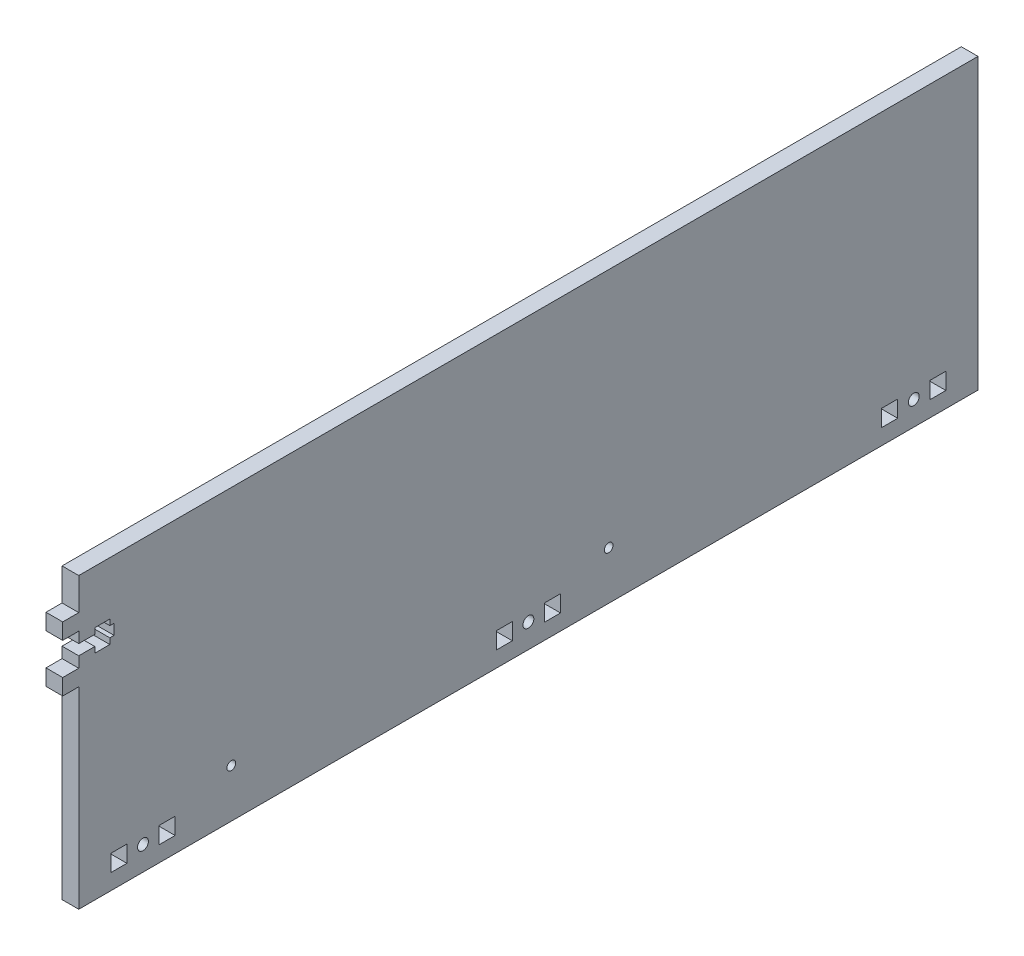
SolidWorks part; units mm, degrees
material "Acrylic (Blue)"
ref_plane "Front Plane" through (0, 0, 0) normal (0, 0, 1) x (1, 0, 0)
ref_plane "Top Plane" through (0, 0, 0) normal (0, 1, 0) x (1, 0, 0)
ref_plane "Right Plane" through (0, 0, 0) normal (1, 0, 0) x (0, 0, -1)
sketch "Sketch1" plane through (0, 0, 0) normal (1, 0, 0) x (0, 0, -1)
  line L0 (-139.7, 12.827) -> (-12.7, 12.827) construction
  line L1 (-177.8, 114.3) -> (177.8, 114.3)
  line L2 (-177.8, 114.3) -> (-177.8, 0)
  line L3 (-177.8, 0) -> (177.8, 0)
  line L4 (177.8, 114.3) -> (177.8, 0)
  line L5 (12.7, 12.827) -> (139.7, 12.827) construction
  line B0 (-146.05, 12.827) -> (-139.7, 12.827)
  line B1 (-139.7, 12.827) -> (-139.7, 6.223)
  line B2 (-139.7, 6.223) -> (-146.05, 6.223)
  line B3 (-146.05, 6.223) -> (-146.05, 12.827)
  line B4 (-165.1, 12.827) -> (-158.75, 12.827)
  line B5 (-158.75, 12.827) -> (-158.75, 6.223)
  line B6 (-158.75, 6.223) -> (-165.1, 6.223)
  line B7 (-165.1, 6.223) -> (-165.1, 12.827)
  circle B8 centre (-152.4, 9.525) radius 2.1526
  line B9 (6.35, 12.827) -> (12.7, 12.827)
  line B10 (12.7, 12.827) -> (12.7, 6.223)
  line B11 (12.7, 6.223) -> (6.35, 6.223)
  line B12 (6.35, 6.223) -> (6.35, 12.827)
  line B13 (-12.7, 12.827) -> (-6.35, 12.827)
  line B14 (-6.35, 12.827) -> (-6.35, 6.223)
  line B15 (-6.35, 6.223) -> (-12.7, 6.223)
  line B16 (-12.7, 6.223) -> (-12.7, 12.827)
  circle B17 centre (0, 9.525) radius 2.1526
  line B18 (158.75, 12.827) -> (165.1, 12.827)
  line B19 (165.1, 12.827) -> (165.1, 6.223)
  line B20 (165.1, 6.223) -> (158.75, 6.223)
  line B21 (158.75, 6.223) -> (158.75, 12.827)
  line B22 (139.7, 12.827) -> (146.05, 12.827)
  line B23 (146.05, 12.827) -> (146.05, 6.223)
  line B24 (146.05, 6.223) -> (139.7, 6.223)
  line B25 (139.7, 6.223) -> (139.7, 12.827)
  circle B26 centre (152.4, 9.525) radius 2.1526
  dimension "D1" = 114.3
  dimension "D2" = 355.6
  dimension "D3" = 12.7
  dimension "D4" = 12.7
  dimension "D5" = 9.525
sketch_block_instance "BOLT_HOLE-1"
sketch_block "BOLT_HOLE" parameters "D1"=4.3053, "D2"=6.35, "D3"=6.35, "D4"=6.604
sketch_block_instance "BOLT_HOLE-2"
sketch_block_instance "BOLT_HOLE-3"
extrude "Boss-Extrude1" add sketch "Sketch1" along normal blind 6.604
sketch "Sketch4" plane through (0, 0, 0) normal (-1, 0, 0) x (0, 0, 1)
  line L0 (177.8, 114.3) -> (177.8, 0) construction
  line L1 (-177.8, 114.3) -> (177.8, 114.3) construction
  line B0 (177.8, 90.9828) -> (171.45, 90.9828)
  line B1 (171.45, 90.9828) -> (171.45, 93.2688)
  line B2 (171.45, 93.2688) -> (165.5064, 93.2688)
  line B3 (165.5064, 93.2688) -> (165.5064, 90.9828)
  line B4 (165.5064, 90.9828) -> (163.83, 90.9828)
  line B5 (163.83, 90.9828) -> (163.83, 86.8172)
  line B6 (163.83, 86.8172) -> (165.5064, 86.8172)
  line B7 (165.5064, 86.8172) -> (165.5064, 84.5312)
  line B8 (165.5064, 84.5312) -> (171.45, 84.5312)
  line B9 (171.45, 84.5312) -> (171.45, 86.8172)
  line B10 (171.45, 86.8172) -> (177.8, 86.8172)
  line B11 (177.8, 86.8172) -> (177.8, 82.55)
  line B12 (177.8, 82.55) -> (184.15, 82.55)
  line B13 (184.15, 82.55) -> (184.15, 76.2)
  line B14 (184.15, 76.2) -> (177.8, 76.2)
  line B15 (177.8, 90.9828) -> (177.8, 95.25)
  line B16 (177.8, 95.25) -> (184.15, 95.25)
  line B17 (184.15, 95.25) -> (184.15, 101.6)
  line B18 (184.15, 101.6) -> (177.8, 101.6)
  line B19 (177.8, 86.8172) -> (177.8, 90.9828) construction
  dimension "D1" = 12.7
sketch_block_instance "NUT_HOLE-1"
sketch_block "NUT_HOLE" parameters "D1"=6.35, "D2"=4.1656, "D3"=25.4, "D4"=6.35, "D5"=8.7376, "D6"=5.9436, "D7"=6.35, "D8"=20.32
sketch "Sketch5" plane through (0, 0, 0) normal (-1, 0, 0) x (0, 0, 1)
  line L0 (177.8, 90.9828) -> (171.45, 90.9828) construction
  line L1 (171.45, 90.9828) -> (171.45, 93.2688) construction
  line L2 (171.45, 93.2688) -> (165.5064, 93.2688) construction
  line L3 (165.5064, 93.2688) -> (165.5064, 90.9828) construction
  line L4 (165.5064, 90.9828) -> (163.83, 90.9828) construction
  line L5 (163.83, 90.9828) -> (163.83, 86.8172) construction
  line L6 (163.83, 86.8172) -> (165.5064, 86.8172) construction
  line L7 (165.5064, 86.8172) -> (165.5064, 84.5312) construction
  line L8 (165.5064, 84.5312) -> (171.45, 84.5312) construction
  line L9 (171.45, 86.8172) -> (177.8, 86.8172) construction
  line L10 (171.45, 84.5312) -> (171.45, 86.8172) construction
  line L11 (177.8, 90.9828) -> (171.45, 90.9828)
  line L12 (171.45, 90.9828) -> (171.45, 93.2688)
  line L13 (171.45, 93.2688) -> (165.5064, 93.2688)
  line L14 (165.5064, 93.2688) -> (165.5064, 90.9828)
  line L15 (165.5064, 90.9828) -> (163.83, 90.9828)
  line L16 (163.83, 90.9828) -> (163.83, 86.8172)
  line L17 (163.83, 86.8172) -> (165.5064, 86.8172)
  line L18 (165.5064, 86.8172) -> (165.5064, 84.5312)
  line L19 (165.5064, 84.5312) -> (171.45, 84.5312)
  line L20 (171.45, 86.8172) -> (177.8, 86.8172)
  line L21 (171.45, 84.5312) -> (171.45, 86.8172)
  line L22 (177.8, 90.9828) -> (177.8, 86.8172)
extrude "Cut-Extrude1" cut sketch "Sketch5" against normal through all
sketch "Sketch6" plane through (0, 0, 0) normal (-1, 0, 0) x (0, 0, 1)
  line L0 (184.15, 101.6) -> (177.8, 101.6) construction
  line L1 (184.15, 95.25) -> (184.15, 101.6) construction
  line L2 (177.8, 95.25) -> (184.15, 95.25) construction
  line L3 (184.15, 76.2) -> (177.8, 76.2) construction
  line L4 (177.8, 82.55) -> (184.15, 82.55) construction
  line L5 (184.15, 82.55) -> (184.15, 76.2) construction
  line L6 (184.15, 101.6) -> (177.8, 101.6)
  line L7 (184.15, 95.25) -> (184.15, 101.6)
  line L8 (177.8, 95.25) -> (184.15, 95.25)
  line L9 (184.15, 76.2) -> (177.8, 76.2)
  line L10 (177.8, 82.55) -> (184.15, 82.55)
  line L11 (184.15, 82.55) -> (184.15, 76.2)
  line L12 (177.8, 101.6) -> (177.8, 95.25)
  line L13 (177.8, 82.55) -> (177.8, 76.2)
extrude "Boss-Extrude2" add sketch "Sketch6" against normal up to surface (6.604 mm away) up to face at (6.604, 80.9625, 126.9428)
hole_wizard "CSK for #8 Flat Head Socket Cap Screw1" positions "Sketch8" profile "Sketch7" countersink size "#8" standard "ANSI Inch" end condition through all
sketch "Sketch8" plane through (0, 0, 0) normal (-1, 0, 0) x (0, 0, 1)
  circle A0 centre (152.4, 9.525) radius 2.1527 construction
  point P0 (-152.4, 9.525)
  point P3 (0, 9.525)
  point P6 (152.4, 9.525)
sketch "Sketch7" plane through (0, 9.525, -152.4) normal (0, 1, 0) x (0, 0, 1)
  line L0 (0, 0) -> (0, 6.604)
  line L1 (0, 6.604) -> (2.1526, 6.604)
  line L2 (2.1526, 6.604) -> (2.1526, 2.7685)
  line L3 (2.1526, 2.7685) -> (4.5593, 0)
  line L5 (4.5593, 0) -> (0, 0)
  line L6 (-2.1526, 2.7685) -> (-4.5593, 0) construction
  line L11 (0, -6.35) -> (0, 107.95) construction
  dimension "Thru Hole Dia." = 4.3053
  dimension "Thru Hole Depth" = 6.604
  dimension "Near C'Sink Dia." = 9.1186
  dimension "Near C'Sink Angle" = 82
hole_wizard "#8-32 Tapped Hole1" positions "Sketch10" profile "Sketch9" tap size "#8-32" standard "ANSI Inch"
sketch "Sketch10" plane through (0, 0, 0) normal (-1, 0, 0) x (0, 0, 1)
  line L0 (176.8025, -3.175) -> (-28.4585, -3.175) construction
  line L2 (177.8, 19.05) -> (117.475, 19.05) construction
  line L3 (177.8, 76.2) -> (177.8, 0) construction
  line L5 (117.475, 19.05) -> (-31.75, 19.05) construction
  line L7 (177.8, 0) -> (-177.8, 0) construction
  point P5 (117.475, 19.05)
  point P11 (-31.75, 19.05)
  dimension "D1" = 3.175
  dimension "D2" = 60.325
  dimension "D3" = 209.55
  dimension "D4" = 22.225
sketch "Sketch9" plane through (0, 19.05, 117.475) normal (0, 1, 0) x (0, 0, 1)
  line L0 (0, 0) -> (0, 11.7566)
  line L1 (0, 11.7566) -> (1.7272, 10.7188)
  line L2 (1.7272, 10.7188) -> (1.7272, 0)
  line L5 (1.7272, 0) -> (0, 0)
  line L10 (0, 11.7566) -> (-1.7272, 10.7188) construction
  line L11 (0, -6.35) -> (0, 107.95) construction
  dimension "Tap Drill Dia." = 3.4544
  dimension "Tap Drill Depth" = 10.7188
  dimension "Drill Angle" = 118
other "Move Face1" [suppressed] parameters "D1"=0.0508
